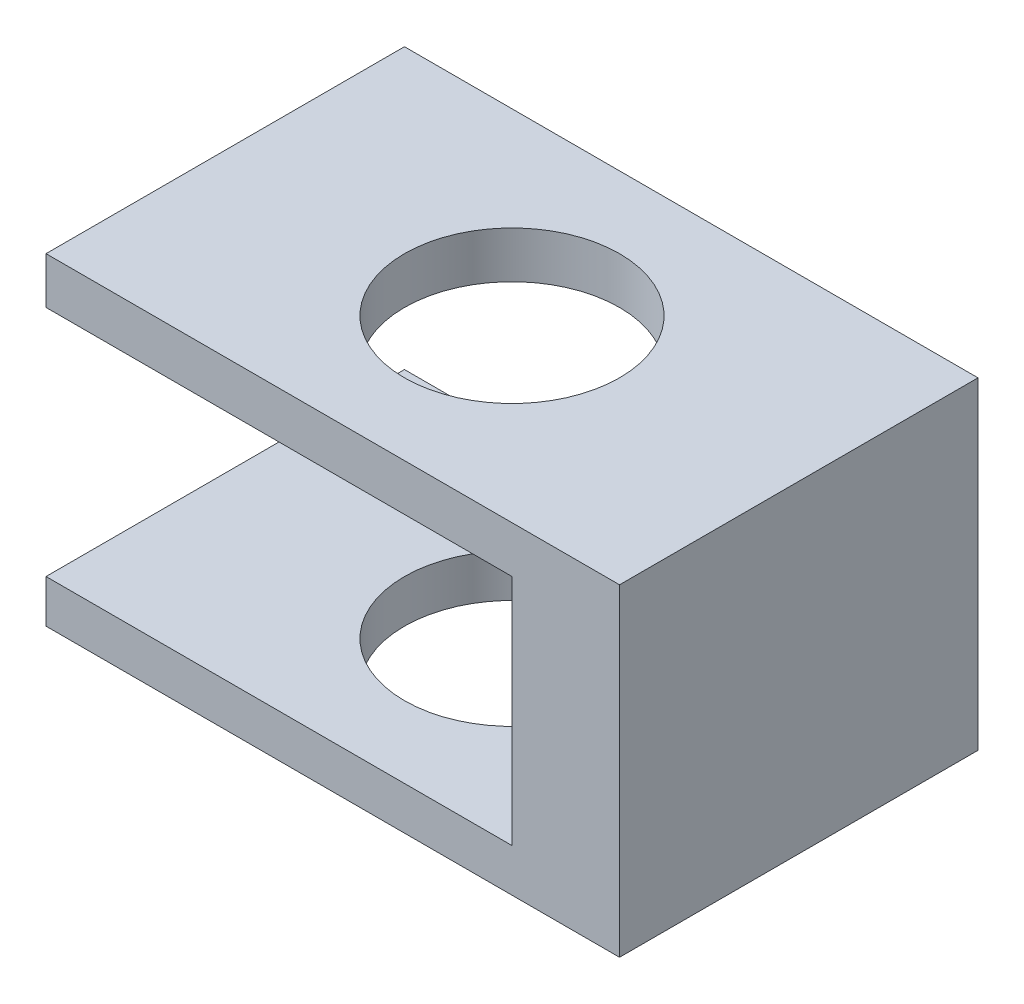
SolidWorks part; units mm, degrees
ref_plane "Front Plane" through (0, 0, 0) normal (0, 0, 1) x (1, 0, 0)
ref_plane "Top Plane" through (0, 0, 0) normal (0, 1, 0) x (1, 0, 0)
ref_plane "Right Plane" through (0, 0, 0) normal (1, 0, 0) x (0, 0, -1)
sketch "Sketch2" plane through (0, 0, 0) normal (0, 0, 1) x (1, 0, 0)
  line L1 (-0.8, 0.45) -> (0.8, 0.45)
  line L2 (-0.8, 0.45) -> (-0.8, -0.45)
  line L3 (-0.8, -0.45) -> (0.8, -0.45)
  line L4 (0.8, 0.45) -> (0.8, -0.45)
  line L5 (-0.8, 0.45) -> (0.8, -0.45) construction
  line L6 (-0.8, -0.45) -> (0.8, 0.45) construction
  point P0 (0, 0)
  dimension "D1" = 1.6
  dimension "D2" = 0.9
extrude "Boss-Extrude2" add sketch "Sketch2" along normal blind 1
sketch "Sketch5" plane through (0, 0.45, 0) normal (0, 1, 0) x (1, 0, 0)
  circle A0 centre (0, -0.5) radius 0.3
extrude "Cut-Extrude2" cut sketch "Sketch5" against normal blind 1
sketch "Sketch6" plane through (0, 0, 1) normal (0, 0, 1) x (1, 0, 0)
  line L0 (0.8, -0.45) -> (0.8, 0.45) construction
  line L1 (-0.5, 0.32) -> (0.5, 0.32)
  line L2 (-0.5, 0.32) -> (-0.5, -0.33)
  line L3 (-0.5, -0.33) -> (0.5, -0.33)
  line L4 (0.5, 0.32) -> (0.5, -0.33)
  line L5 (-0.8, -0.45) -> (0.8, -0.45) construction
  dimension "D1" = 1
  dimension "D2" = 0.65
  dimension "D3" = 0.3
  dimension "D4" = 0.12
extrude "Cut-Extrude3" cut sketch "Sketch6" against normal blind 0.8
sketch "Sketch7" plane through (0, 0, 1) normal (0, 0, 1) x (1, 0, 0)
  line L0 (-0.5, 0.32) -> (-0.8768, 0.32) construction
  line L1 (-0.8, 0.45) -> (-0.8, -0.45) construction
  line L2 (-0.8, 0.32) -> (0.5, 0.32)
  line L3 (-0.8, 0.32) -> (-0.8, -0.33)
  line L4 (-0.8, -0.33) -> (0.5, -0.33)
  line L5 (0.5, 0.32) -> (0.5, -0.33)
extrude "Cut-Extrude4" cut sketch "Sketch7" against normal blind 1
